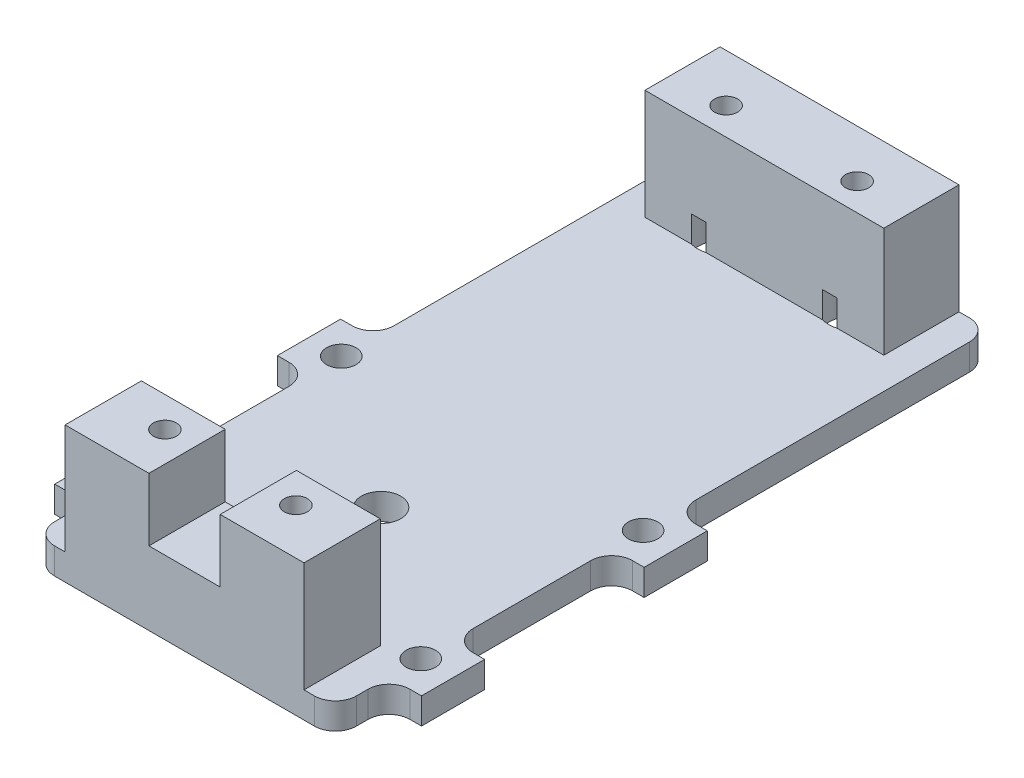
SolidWorks part; units mm, degrees
material "ABS"
ref_plane "Front Plane" through (0, 0, 0) normal (0, 0, 1) x (1, 0, 0)
ref_plane "Top Plane" through (0, 0, 0) normal (0, 1, 0) x (1, 0, 0)
ref_plane "Right Plane" through (0, 0, 0) normal (1, 0, 0) x (0, 0, -1)
sketch "Sketch1" plane through (0, 0, 0) normal (0, 1, 0) x (1, 0, 0)
  line L0 (18.288, -9.6647) -> (22.225, -9.6647)
  line L1 (-18.288, -23.8125) -> (18.288, -23.8125)
  line L2 (-18.288, -23.8125) -> (-18.288, -17.3228)
  line L3 (-18.288, 55.5625) -> (18.288, 55.5625)
  line L4 (18.288, -23.8125) -> (18.288, -17.3228)
  line L5 (-22.225, -17.3228) -> (-18.288, -17.3228)
  line L6 (-22.225, -17.3228) -> (-22.225, -9.6647)
  line L7 (-22.225, 17.3228) -> (-18.288, 17.3228)
  line L8 (22.225, -17.3228) -> (22.225, -9.6647)
  line L9 (0, 0.0043) -> (-31.7584, 0.0043) construction
  line L10 (-31.7584, 0.0043) -> (-18.288, -13.4661) construction
  line L11 (-22.225, -9.6647) -> (-18.288, -9.6647)
  line L12 (-18.288, 17.3228) -> (-18.288, 55.5625)
  line L13 (-22.225, 9.6647) -> (-18.288, 9.6647)
  line L14 (-18.288, -9.6647) -> (-18.288, 9.6647)
  line L15 (18.288, 9.6647) -> (22.225, 9.6647)
  line L17 (18.288, -9.6647) -> (18.288, 9.6647)
  line L18 (22.225, 9.6647) -> (22.225, 17.3228)
  line L19 (-22.225, 9.6647) -> (-22.225, 17.3228)
  line L20 (-18.288, -9.6647) -> (-18.288, 9.6647)
  line L21 (18.288, -9.6647) -> (18.288, 9.6647)
  line L22 (18.288, 17.3228) -> (18.288, 55.5625)
  line L23 (18.288, 17.3228) -> (22.225, 17.3228)
  line L24 (18.288, -17.3228) -> (22.225, -17.3228)
  line L25 (-31.7584, 0.0043) -> (-18.288, 13.4747) construction
  line L26 (0, -23.8125) -> (0, 0.0043) construction
  line L28 (-14.478, -13.8906) -> (14.478, -13.8906) construction
  line L29 (-14.478, -13.8906) -> (-14.478, 45.7994) construction
  line L30 (-14.478, 45.7994) -> (14.478, 45.7994) construction
  line L31 (14.478, -13.8906) -> (14.478, 45.7994) construction
  circle A0 centre (0, 0.0043) radius 2.3813
  circle A1 centre (7.9375, 49.7649) radius 3.429 construction
  circle A2 centre (-7.9375, 49.7649) radius 3.429 construction
  circle A3 centre (7.9375, -18.2563) radius 3.429 construction
  circle A4 centre (-7.9375, -18.2563) radius 3.429 construction
  point P4 (-7.9375, -18.2562)
  point P6 (0, 0)
  point P9 (7.9375, -18.2562)
  point P10 (-7.9375, 49.7649)
  point P11 (7.9375, 49.7649)
  point P31 (18.288, -13.4661)
  point P32 (18.288, 13.4747)
  dimension "D21" = 6.858
  dimension "D1" = 36.576
  dimension "D2" = 79.375
  dimension "D3" = 18.288
  dimension "D4" = 23.8125
  dimension "D5" = 18.2562
  dimension "D6" = 7.9375
  dimension "D9" = 5.5563
  dimension "D10" = 34.6456
  dimension "D11" = 44.45
  dimension "D12" = 19.3294
  dimension "D13" = 9.6647
  dimension "D14" = 19.05
  dimension "D15" = 19.05
  dimension "D16" = 90
  dimension "D17" = 28.956
  dimension "D18" = 14.478
  dimension "D19" = 59.69
  dimension "D20" = 13.8906
  dimension "D7" = 2
  dimension "D8" = 2
extrude "Boss-Extrude1" add sketch "Sketch1" along normal blind 3.175 contours L4 L24 L8 L0 L17 L15 L18 L23 L22 L3 L12 L7 L19 L13 L14 L11 L6 L5 L2 L1 L31 L28 L29 L30
hole_wizard "9/64 (0.14063) Diameter Hole1" positions "Sketch5" profile "Sketch6" hole size "9/64" standard "Ansi Inch" end condition up to next
sketch "Sketch5" plane through (0, 0, 0) normal (0, -1, 0) x (1, 0, 0)
  point P4 (18.288, -13.4747)
  point P7 (18.288, 13.4661)
  point P35 (-18.288, -13.4704)
  point P37 (-18.288, 13.4704)
sketch "Sketch6" plane through (18.288, 0, -13.4747) normal (1, 0, 0) x (0, 0, -1)
  line L0 (0, 0) -> (0, 3.175)
  line L1 (0, 3.175) -> (1.786, 3.175)
  line L2 (1.786, 3.175) -> (1.786, 0)
  line L5 (1.786, 0) -> (0, 0)
  line L11 (0, -6.35) -> (0, 107.95) construction
  dimension "Thru Hole Dia." = 3.572
  dimension "Thru Hole Depth" = 3.175
fillet "Fillet1" radius 2.54 12 edges at (18.288, 1.5875, 23.8125) (18.288, 1.5875, 17.3228) (18.288, 1.5875, 9.6647) (18.288, 1.5875, -9.6647) (18.288, 1.5875, -17.3228) (18.288, 1.5875, -55.5625) (-18.288, 1.5875, -55.5625) (-18.288, 1.5875, -17.3228) (-18.288, 1.5875, -9.6647) (-18.288, 1.5875, 9.6647) (-18.288, 1.5875, 17.3228) (-18.288, 1.5875, 23.8125)
sketch "Sketch9" plane through (0, 0, 0) normal (0, 1, 0) x (1, 0, 0)
  line L0 (-18.288, 55.5625) -> (18.288, 55.5625) construction
  line L1 (-18.288, -23.8125) -> (18.288, -23.8125) construction
  line L5 (-14.478, -14.5696) -> (14.478, -14.5696)
  line L6 (-14.478, -14.5696) -> (-14.478, -23.8125)
  line L8 (-14.4653, 46.453) -> (14.4907, 46.453)
  line L9 (-14.4653, 46.453) -> (-14.4653, 55.5625)
  line L10 (-14.4653, 55.5625) -> (14.4907, 55.5625)
  line L11 (14.4907, 46.453) -> (14.4907, 55.5625)
  line L12 (-14.478, -23.8125) -> (14.478, -23.8125)
  line L13 (14.478, -14.5696) -> (14.478, -23.8125)
  circle A2 centre (-7.9375, -18.2562) radius 1.397
  circle A3 centre (7.9375, -18.2562) radius 1.397
  circle A4 centre (-7.9375, 49.7649) radius 1.397
  circle A5 centre (7.9375, 49.7649) radius 1.397
  dimension "D1" = 2.794
  dimension "D2" = 2.794
  dimension "D3" = 2.794
  dimension "D4" = 2.794
  dimension "D5" = 9.1095
  dimension "D7" = 28.956
  dimension "D8" = 9.2429
extrude "Boss-Extrude3" add sketch "Sketch9" along normal blind 16.51
sketch "Sketch10" plane through (0, 0, 0) normal (0, -1, 0) x (1, 0, 0)
  circle A0 centre (7.9375, 18.2562) radius 3.429
  circle A1 centre (-7.9375, 18.2562) radius 3.429
  circle A2 centre (7.9375, -49.7649) radius 3.429
  circle A3 centre (-7.9375, -49.7649) radius 3.429
extrude "Cut-Extrude1" cut sketch "Sketch10" against normal blind 6.35
sketch "Sketch11" plane through (0, 16.51, 0) normal (0, 1, 0) x (1, 0, 0)
  line L1 (-4.318, -14.5696) -> (4.318, -14.5696)
  line L2 (-4.318, -14.5696) -> (-4.318, -23.8125)
  line L3 (-4.318, -23.8125) -> (4.318, -23.8125)
  line L4 (4.318, -14.5696) -> (4.318, -23.8125)
  line L5 (-14.478, -14.5696) -> (-14.478, -23.8125) construction
  line L6 (14.478, -23.8125) -> (14.478, -14.5696) construction
  point P7 (-14.478, -19.191)
  dimension "D1" = 8.636
  dimension "D2" = 10.16
  dimension "D3" = 10.16
extrude "Cut-Extrude2" cut sketch "Sketch11" against normal blind 7.62
